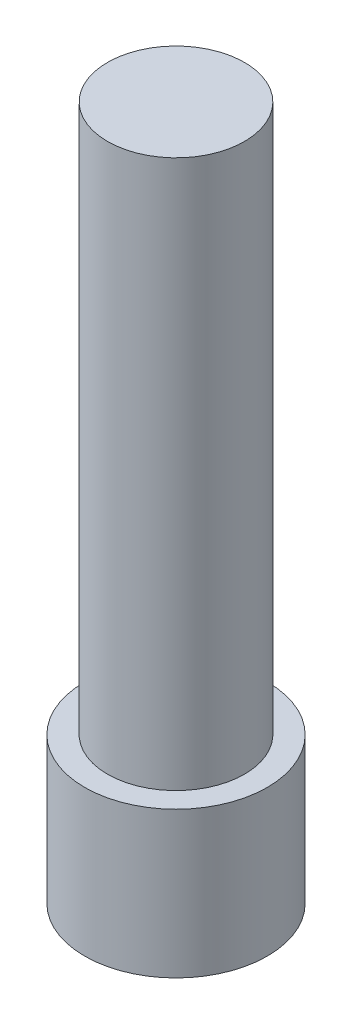
SolidWorks part; units mm, degrees
ref_plane "Front Plane" through (0, 0, 0) normal (0, 0, 1) x (1, 0, 0)
ref_plane "Top Plane" through (0, 0, 0) normal (0, 1, 0) x (1, 0, 0)
ref_plane "Right Plane" through (0, 0, 0) normal (1, 0, 0) x (0, 0, -1)
sketch "Sketch1" plane through (0, 0, 0) normal (0, 1, 0) x (1, 0, 0)
  circle A0 centre (0, 0) radius 37.5
  dimension "D1" = 75
extrude "Boss-Extrude1" add sketch "Sketch1" along normal blind 300 contours A0
sketch "Sketch2" plane through (0, 0, 0) normal (0, 1, 0) x (1, 0, 0)
  circle A0 centre (0, 0) radius 50
  dimension "D1" = 100
extrude "Boss-Extrude2" add sketch "Sketch2" against normal blind 80
